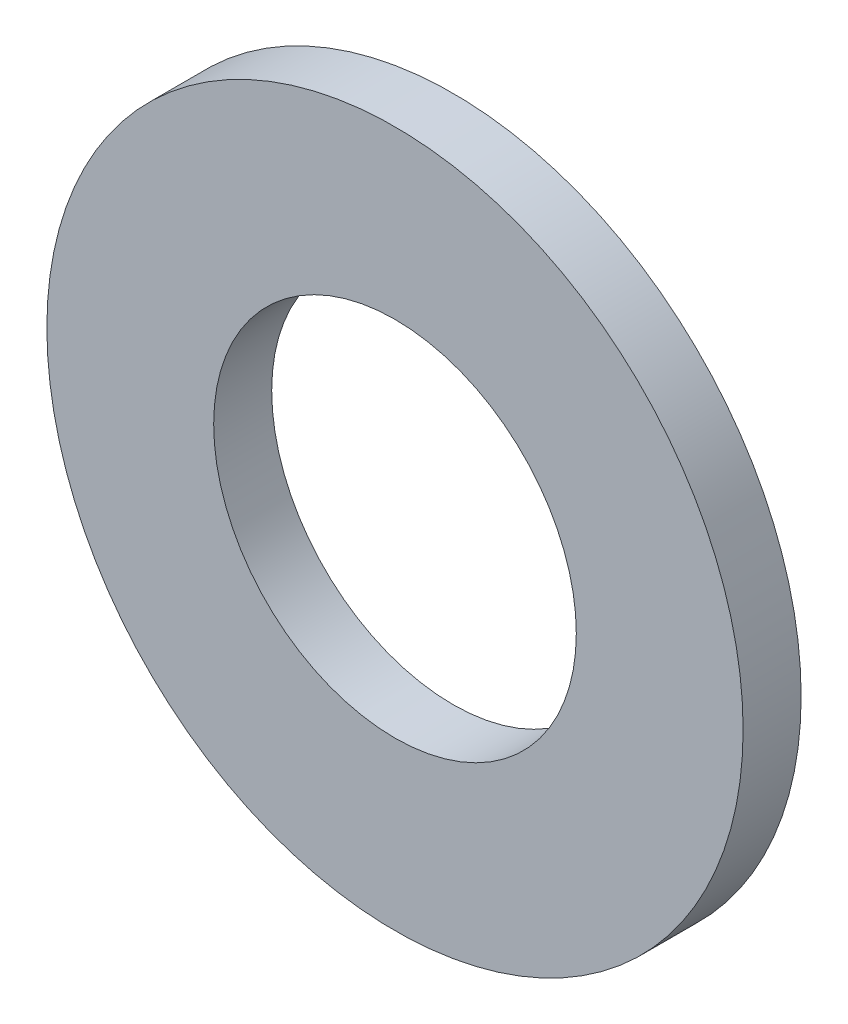
SolidWorks part; units mm, degrees
ref_plane "Front Plane" through (0, 0, 0) normal (0, 0, 1) x (1, 0, 0)
ref_plane "Top Plane" through (0, 0, 0) normal (0, 1, 0) x (1, 0, 0)
ref_plane "Right Plane" through (0, 0, 0) normal (1, 0, 0) x (0, 0, -1)
sketch "Sketch1" plane through (0, 0, 0) normal (0, 0, 1) x (1, 0, 0)
  circle A0 centre (0, 0) radius 6
  circle A1 centre (0, 0) radius 3.125
  dimension "D1" = 12
  dimension "D2" = 6.25
extrude "Boss-Extrude1" add sketch "Sketch1" along normal blind 1
